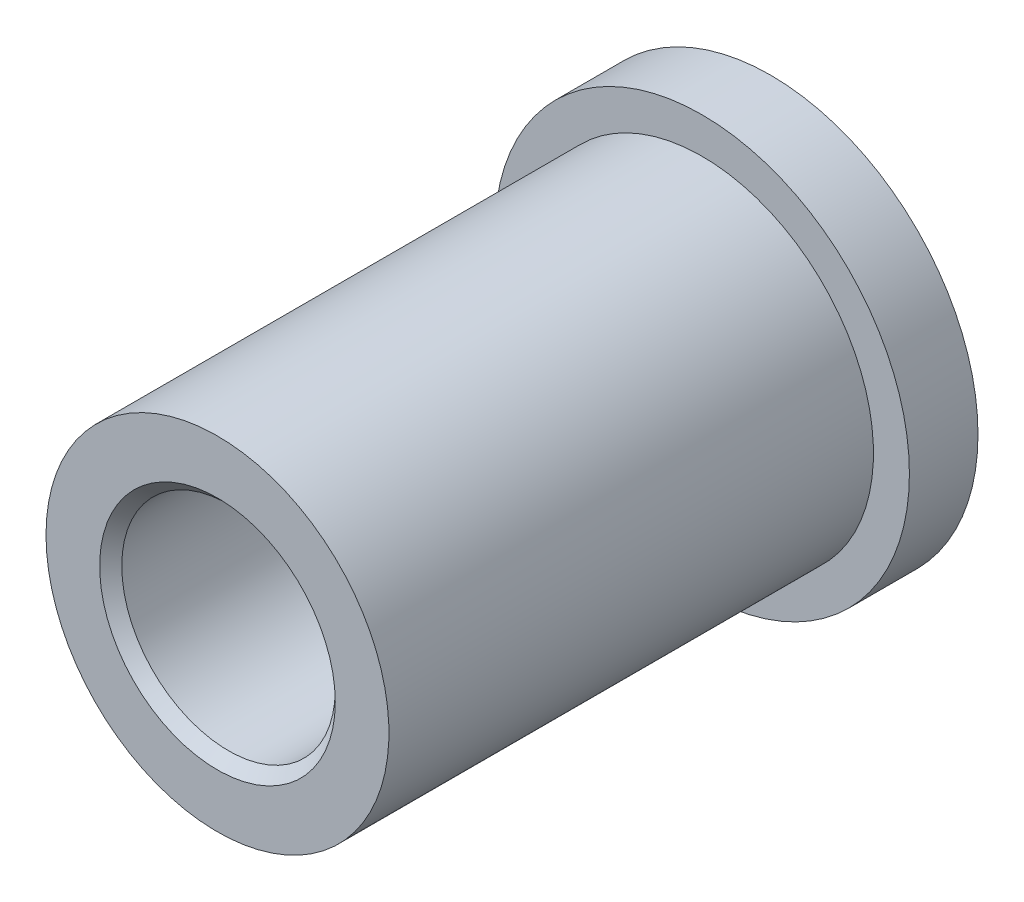
SolidWorks part; units mm, degrees
ref_plane "Front Plane" through (0, 0, 0) normal (0, 0, 1) x (1, 0, 0)
ref_plane "Top Plane" through (0, 0, 0) normal (0, 1, 0) x (1, 0, 0)
ref_plane "Right Plane" through (0, 0, 0) normal (1, 0, 0) x (0, 0, -1)
sketch "Sketch1" plane through (0, 0, 0) normal (0, 1, 0) x (1, 0, 0)
  line L0 (0, 0) -> (0, 12.7)
  line L1 (0, 12.7) -> (-2.3114, 12.7)
  line L2 (-2.3114, 12.7) -> (-2.3114, 11.1252)
  line L3 (-2.3114, 11.1252) -> (-1.4859, 11.1252)
  line L4 (-1.4859, 11.1252) -> (-1.4859, 0)
  line L5 (-1.4859, 0) -> (0, 0)
  line L6 (2.4511, 12.7) -> (2.4511, 0)
  dimension "D1" = 12.7
  dimension "D2" = 1.5748
  dimension "D3" = 4.7625
  dimension "D4" = 3.937
revolve "Revolve1" add sketch "Sketch1" angle 360 about L6
chamfer "Chamfer1" distance 0.254 angle 45 2 edges at (0, 0, 0) (0, 0, -12.7)
